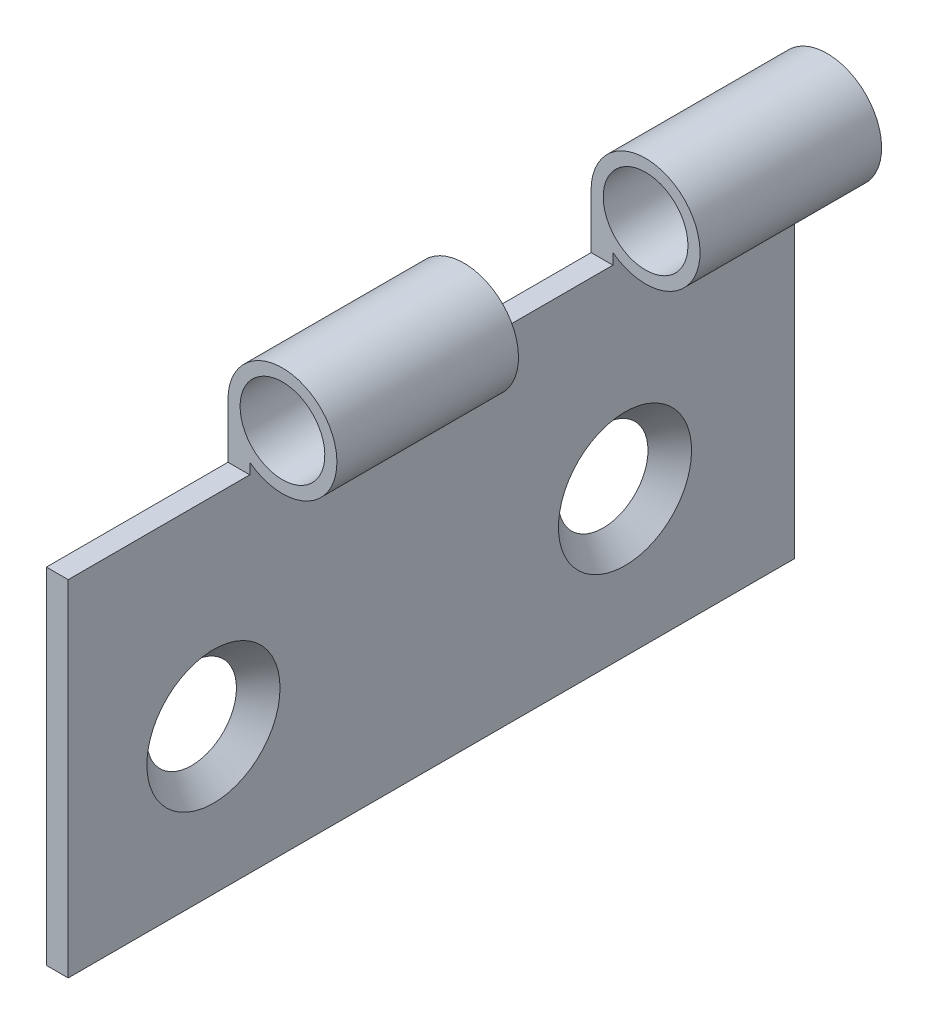
SolidWorks part; units mm, degrees
ref_plane "Piano frontale" through (0, 0, 0) normal (0, 0, 1) x (1, 0, 0)
ref_plane "Piano superiore" through (0, 0, 0) normal (0, 1, 0) x (1, 0, 0)
ref_plane "Piano destro" through (0, 0, 0) normal (1, 0, 0) x (0, 0, -1)
sketch "Schizzo1" plane through (0, 0, 0) normal (0, 0, 1) x (1, 0, 0)
  line L0 (0, 0) -> (0, 16.5)
  dimension "D1" = 16.5
extrude "Estrusione-Sottile1" add sketch "Schizzo1" along normal mid plane 30 thin
sketch "Schizzo2" plane through (0, 0, 15) normal (0, 0, 1) x (1, 0, 0)
  line L0 (0, 16.5) -> (18.142, 16.5) construction
  circle A0 centre (2.25, 16.5) radius 2.25
  dimension "D1" = 4.5
sweep "Sweep1" add profiles "Schizzo2" path edge at (0.9, 16.5, 0)
sketch "Schizzo4" plane through (0, 0, 15) normal (0, 0, 1) x (1, 0, 0)
  circle A0 centre (2.25, 16.5) radius 1.75
  dimension "D1" = 3.5
extrude "Taglio-Estrusione1" cut sketch "Schizzo4" against normal through all
sketch "Schizzo3" plane through (0.9, 0, 0) normal (1, 0, 0) x (0, 0, -1)
  line L2 (-7.5, 14.25) -> (0, 14.25)
  line L3 (-7.5, 14.25) -> (-7.5, 18.75)
  line L4 (-7.5, 18.75) -> (0, 18.75)
  line L5 (0, 14.25) -> (0, 18.75)
  line L6 (7.5, 14.25) -> (15, 14.25)
  line L7 (7.5, 14.25) -> (7.5, 18.75)
  line L8 (-7.5, 14.25) -> (0, 14.25)
  line L9 (7.5, 18.75) -> (15, 18.75)
  line L10 (15, 14.25) -> (15, 18.75)
  line L11 (15, 14.25) -> (15, 18.75) construction
  line L12 (-7.5, 14.25) -> (0, 14.25)
  line L13 (15, 14.25) -> (15, 18.75)
  line L14 (-7.5, 14.25) -> (-7.5, 18.75)
  line L15 (-7.5, 18.75) -> (0, 18.75)
  line L16 (0, 14.25) -> (0, 18.75)
  line L22 (-7.5, 18.75) -> (0, 18.75)
  line L23 (-7.5, 14.25) -> (-7.5, 18.75)
  line L24 (0, 14.25) -> (0, 18.75)
  line L25 (7.5, 14.25) -> (7.5, 18.75)
  line L28 (7.5, 18.75) -> (15, 18.75)
  line L29 (7.5, 14.25) -> (15, 14.25)
  dimension "D2" = 7.5
  dimension "D1" = 4.5
  dimension "D3" = 7.5
sketch "Schizzo7" plane through (0, 0, 0) normal (-1, 0, 0) x (0, 0, 1)
  line L5 (-15, 14.25) -> (15, 14.25) construction
  line L6 (15, 18.75) -> (7.5, 18.75)
  line L7 (15, 18.75) -> (15, 14.25)
  line L8 (15, 14.25) -> (7.5, 14.25)
  line L9 (7.5, 18.75) -> (7.5, 14.25)
  line L11 (0, 18.75) -> (-7.5, 18.75)
  line L12 (0, 18.75) -> (0, 14.25)
  line L13 (0, 14.25) -> (-7.5, 14.25)
  line L14 (-7.5, 18.75) -> (-7.5, 14.25)
  dimension "D1" = 7.5
  dimension "D2" = 7.5
  dimension "D3" = 7.5
extrude "Taglio-Estrusione13" cut sketch "Schizzo7" against normal blind 10
hole_wizard "Foro svasato per Vite M2.5-1" positions "Schizzo10" profile "Schizzo8" countersink size "M2.5" standard "Ansi Metric" end condition through all
sketch "Schizzo10" plane through (0.9, 0, 0) normal (1, 0, 0) x (0, 0, -1)
  line L0 (-15, 0) -> (-15, 14.25) construction
  line L1 (15, 0) -> (15, 14.7) construction
  line L2 (-15, 0) -> (15, 0) construction
  point P0 (-9, 6)
  point P2 (8, 6)
  dimension "D1" = 6
  dimension "D2" = 7
  dimension "D3" = 6
sketch "Schizzo8" plane through (0.9, 6, 9) normal (0, 1, 0) x (0, 0, -1)
  line L0 (0, 0) -> (0, 0.9)
  line L1 (0, 0.9) -> (1.45, 0.9)
  line L2 (1.45, 0.9) -> (1.45, 1.3)
  line L3 (1.45, 1.3) -> (2.75, 0)
  line L5 (2.75, 0) -> (0, 0)
  line L6 (-1.45, 1.3) -> (-2.75, 0) construction
  line L11 (0, -6.35) -> (0, 107.95) construction
  dimension "Thru Hole Dia." = 2.9
  dimension "Thru Hole Depth" = 0.9
  dimension "Near C'Sink Dia." = 5.5
  dimension "Near C'Sink Angle" = 90
equation "\"Taglio\"= \"Lunghezza\" / 4"
equation "\"D2@Schizzo3\"=\"Taglio\""
equation "\"D3@Schizzo3\"=\"Taglio\""
equation "\"Spess\"= 0.9"
equation "\"D5@Estrusione-Sottile1\"=\"Spess\""
equation "\"Lunghezza\"=30"
equation "\"D1@Estrusione-Sottile1\"=\"Lunghezza\""
equation "\"D1@Schizzo7\"=\"Taglio\""
equation "\"D2@Schizzo7\"=\"Taglio\""
equation "\"D3@Schizzo7\"=\"Taglio\""
